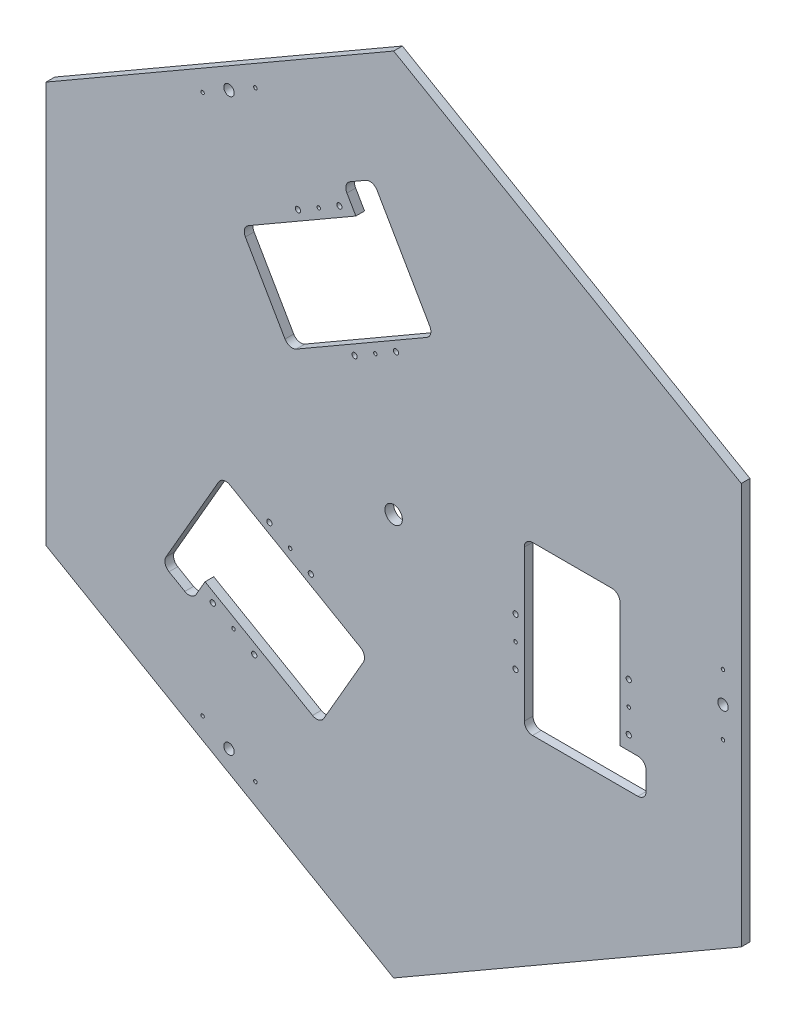
SolidWorks part; units mm, degrees
material "3.0255 (EN-AW 1350A)"
ref_plane "Plan de face" through (0, 0, 0) normal (0, 0, 1) x (1, 0, 0)
ref_plane "Plan de dessus" through (0, 0, 0) normal (0, 1, 0) x (1, 0, 0)
ref_plane "Plan de droite" through (0, 0, 0) normal (1, 0, 0) x (0, 0, -1)
sketch "Esquisse1" plane through (0, 0, 0) normal (0, 0, 1) x (1, 0, 0)
  line L0 (150, 43.9042) -> (150, -49.8787) construction
  line L1 (399.2377, 230.5) -> (0, 461)
  line L2 (0, 461) -> (-399.2377, 230.5)
  line L3 (-399.2377, 230.5) -> (-399.2377, -230.5)
  line L4 (-399.2377, -230.5) -> (0, -461)
  line L5 (0, -461) -> (399.2377, -230.5)
  line L6 (399.2377, -230.5) -> (399.2377, 230.5)
  line L7 (-33.0621, 0) -> (470.8066, 0) construction
  line L8 (150, 42.5) -> (150, -130.5)
  line L9 (159.5, -140) -> (280.5, -140)
  line L10 (290, -130.5) -> (290, -109.5)
  line L11 (280.5, -100) -> (260, -100)
  line L12 (260, -100) -> (260, 42.5)
  line L13 (250.5, 52) -> (159.5, 52)
  line L14 (140, 43.5) -> (140, -118) construction
  line L15 (270, 30.8497) -> (270, -84.7083) construction
  line L16 (205, 52) -> (205, 0) construction
  line L17 (378.2377, 54.7012) -> (378.2377, -44.8259) construction
  line L18 (-80.2167, -242.9394) -> (-34.7167, -164.1311)
  line L19 (-38.1939, -151.1538) -> (-188.0163, -64.6538)
  line L20 (-216.6025, -175.1666) -> (-93.1939, -246.4166)
  line L21 (-200.9936, -68.1311) -> (-261.4936, -172.9201)
  line L22 (-258.0163, -185.8974) -> (-239.8298, -196.3974)
  line L23 (-226.8525, -192.9201) -> (-216.6025, -175.1666)
  line L24 (16.5311, 28.6326) -> (-235.4033, -407.7304) construction
  line L25 (-170.2833, 190.9394) -> (-124.7833, 112.1311)
  line L26 (-111.8061, 108.6538) -> (38.0163, 195.1538)
  line L27 (-43.3975, 275.1666) -> (-166.8061, 203.9166)
  line L28 (41.4936, 208.1311) -> (-19.0064, 312.9201)
  line L29 (-31.9837, 316.3974) -> (-50.1702, 305.8974)
  line L30 (-53.6475, 292.9201) -> (-43.3975, 275.1666)
  line L31 (16.5311, -28.6326) -> (-235.4033, 407.7304) construction
  circle A0 centre (0, 0) radius 399.2377 construction
  circle A1 centre (0, 0) radius 10
  arc A2 (150, -130.5) -> (159.5, -140) centre (159.5, -130.5) ccw
  arc A3 (280.5, -140) -> (290, -130.5) centre (280.5, -130.5) ccw
  arc A4 (290, -109.5) -> (280.5, -100) centre (280.5, -109.5) ccw
  arc A5 (260, 42.5) -> (250.5, 52) centre (250.5, 42.5) ccw
  arc A6 (159.5, 52) -> (150, 42.5) centre (159.5, 42.5) ccw
  circle A7 centre (140, -29) radius 3
  circle A8 centre (140, -56.5) radius 2
  circle A9 centre (140, -84) radius 3
  circle A10 centre (378.2377, 0) radius 6
  circle A11 centre (378.2377, 35) radius 2
  circle A12 centre (378.2377, -35) radius 2
  circle A13 centre (270, -84) radius 3
  circle A14 centre (270, -56.5) radius 2
  circle A15 centre (270, -29) radius 3
  arc A16 (-34.7167, -164.1311) -> (-38.1939, -151.1538) centre (-42.9439, -159.3811) ccw
  arc A17 (-93.1939, -246.4166) -> (-80.2167, -242.9394) centre (-88.4439, -238.1894) ccw
  circle A18 centre (-95.1147, -106.7436) radius 3
  circle A19 centre (-118.9304, -92.9936) radius 2
  circle A20 centre (-142.7461, -79.2436) radius 3
  arc A21 (-188.0163, -64.6538) -> (-200.9936, -68.1311) centre (-192.7663, -72.8811) ccw
  arc A22 (-261.4936, -172.9201) -> (-258.0163, -185.8974) centre (-253.2663, -177.6701) ccw
  arc A23 (-239.8298, -196.3974) -> (-226.8525, -192.9201) centre (-235.0798, -188.1701) ccw
  circle A24 centre (-207.7461, -191.8269) radius 3
  circle A25 centre (-183.9304, -205.5769) radius 2
  circle A26 centre (-160.1147, -219.3269) radius 3
  circle A27 centre (-189.1189, -327.5635) radius 6
  circle A28 centre (-158.808, -345.0635) radius 2
  circle A29 centre (-219.4297, -310.0635) radius 2
  arc A30 (-124.7833, 112.1311) -> (-111.8061, 108.6538) centre (-116.5561, 116.8811) ccw
  arc A31 (-166.8061, 203.9166) -> (-170.2833, 190.9394) centre (-162.0561, 195.6894) ccw
  circle A32 centre (-44.8853, 135.7436) radius 3
  circle A33 centre (-21.0696, 149.4936) radius 2
  circle A34 centre (2.7461, 163.2436) radius 3
  arc A35 (38.0163, 195.1538) -> (41.4936, 208.1311) centre (33.2663, 203.3811) ccw
  arc A36 (-19.0064, 312.9201) -> (-31.9837, 316.3974) centre (-27.2337, 308.1701) ccw
  arc A37 (-50.1702, 305.8974) -> (-53.6475, 292.9201) centre (-45.4202, 297.6701) ccw
  circle A38 centre (-62.2539, 275.8269) radius 3
  circle A39 centre (-86.0696, 262.0769) radius 2
  circle A40 centre (-109.8853, 248.3269) radius 3
  circle A41 centre (-189.1189, 327.5635) radius 6
  circle A42 centre (-219.4297, 310.0635) radius 2
  circle A43 centre (-158.808, 345.0635) radius 2
  point P22 (150, -140)
  point P25 (290, -140)
  point P28 (290, -100)
  point P31 (260, 52)
  point P34 (150, 52)
  point P136 (0, 0)
  dimension "D2" = 20
  dimension "D9" = 9.5
  dimension "D12" = 6
  dimension "D13" = 4
  dimension "D14" = 6
  dimension "D18" = 4
  dimension "D19" = 4
  dimension "D20" = 12
  dimension "D1" = 461
  dimension "D3" = 150
  dimension "D4" = 192
  dimension "D5" = 42.5
  dimension "D6" = 110
  dimension "D7" = 40
  dimension "D8" = 140
  dimension "D10" = 10
  dimension "D11" = 130
  dimension "D15" = 56.5
  dimension "D16" = 29
  dimension "D17" = 55
  dimension "D21" = 21
  dimension "D22" = 35
  dimension "D23" = 35
  dimension "D24" = 3
extrude "Boss.-Extru.1" add sketch "Esquisse1" along normal blind 10
